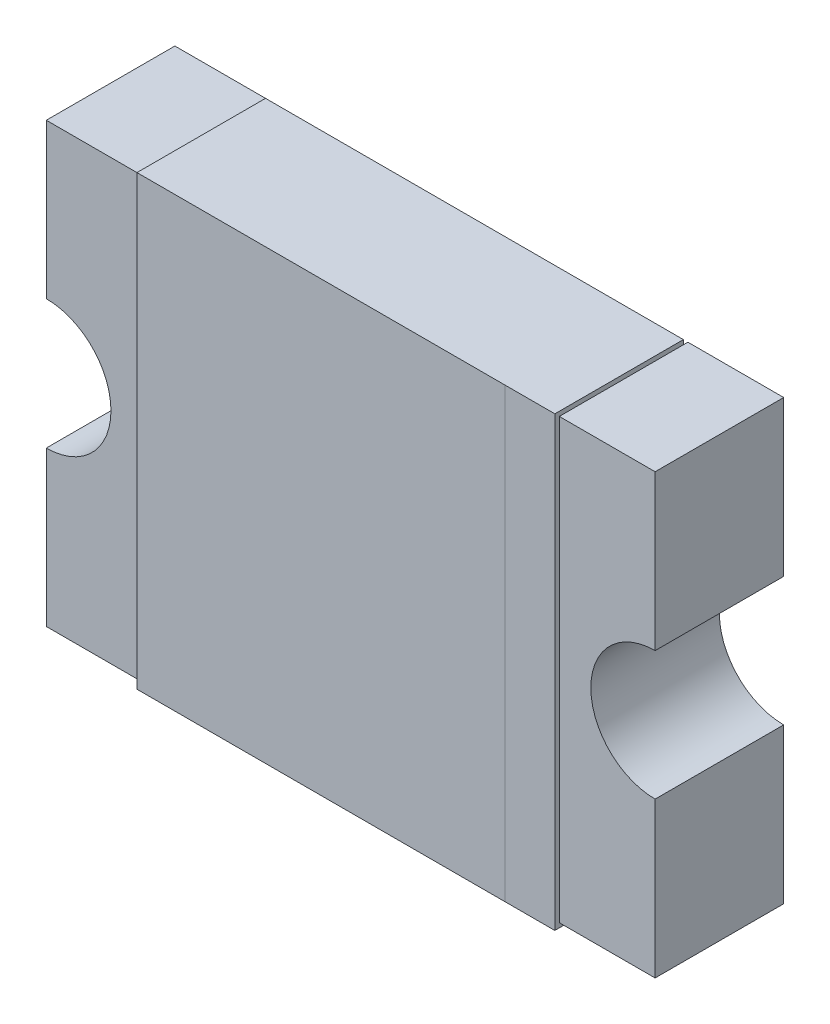
SolidWorks part; units mm, degrees
ref_plane "Plan de face" through (0, 0, 0) normal (0, 0, 1) x (1, 0, 0)
ref_plane "Plan de dessus" through (0, 0, 0) normal (0, 1, 0) x (1, 0, 0)
ref_plane "Plan de droite" through (0, 0, 0) normal (1, 0, 0) x (0, 0, -1)
sketch "Esquisse1" plane through (0, 0, 0) normal (0, 0, 1) x (1, 0, 0)
  line L1 (-2.365, 1.705) -> (2.37, 1.705)
  line L2 (-2.365, 1.705) -> (-2.365, -1.705)
  line L3 (-2.365, -1.705) -> (2.37, -1.705)
  line L4 (2.37, 1.705) -> (2.37, -1.705)
  dimension "D1" = 2.365
  dimension "D2" = 2.37
  dimension "D3" = 1.705
extrude "Extrusion1" add sketch "Esquisse1" along normal blind 1
sketch "Esquisse2" plane through (1.48, 0, 1) normal (0, 0, -1) x (0, 1, 0)
  line L0 (-1.705, 0.89) -> (1.705, 0.89) construction
  circle A0 centre (0, 0.89) radius 0.5
extrude "Enlèv. mat.-Extru.1" cut sketch "Esquisse2" along normal up to vertex (1 mm away)
sketch "Esquisse4" plane through (0, 0, 1) normal (0, 0, 1) x (1, 0, 0)
  line L0 (-2.365, 1.705) -> (-2.365, -1.705) construction
  circle A0 centre (-2.365, 0) radius 0.5029
extrude "Enlèv. mat.-Extru.2" cut sketch "Esquisse4" against normal up to vertex (1 mm away)
sketch "Esquisse8" plane through (0, 0, 1) normal (0, 0, 1) x (1, 0, 0)
  line L0 (2.37, 1.705) -> (-2.365, 1.705) construction
  line L1 (1.625, 1.705) -> (-1.625, 1.705)
  line L2 (1.625, 1.705) -> (1.625, -1.705)
  line L3 (1.625, -1.705) -> (-1.625, -1.705)
  line L4 (-1.625, 1.705) -> (-1.625, -1.705)
  line L5 (-2.365, -1.705) -> (2.37, -1.705) construction
  dimension "D1" = 1.625
  dimension "D2" = 3.25
extrude "Extrusion3" add sketch "Esquisse8" along normal blind 0.035
sketch "Esquisse10" plane through (0, 1.705, 0) normal (0, 1, 0) x (-1, 0, 0)
  line L0 (-2.37, 0) -> (2.365, 0) construction
  line L1 (1.625, 1.035) -> (-1.625, 1.035)
  line L2 (1.625, 1.035) -> (1.625, 0)
  line L3 (1.625, 0) -> (-1.625, 0)
  line L4 (-1.625, 1.035) -> (-1.625, 0)
extrude "Extrusion5" add sketch "Esquisse10" along normal blind 0.035
sketch "Esquisse11" plane through (0, -1.705, 0) normal (0, -1, 0) x (1, 0, 0)
  line L0 (-2.365, 0) -> (2.37, 0) construction
  line L1 (-1.625, 1.035) -> (1.625, 1.035)
  line L2 (-1.625, 1.035) -> (-1.625, 0)
  line L3 (-1.625, 0) -> (1.625, 0)
  line L4 (1.625, 1.035) -> (1.625, 0)
extrude "Extrusion6" add sketch "Esquisse11" along normal blind 0.035
sketch "Esquisse12" plane through (0, 0, 0) normal (0, 0, -1) x (1, 0, 0)
  line L1 (-1.625, 1.74) -> (1.625, 1.74)
  line L2 (-1.625, 1.74) -> (-1.625, -1.74)
  line L3 (-1.625, -1.74) -> (1.625, -1.74)
  line L4 (1.625, 1.74) -> (1.625, -1.74)
extrude "Enlèv. mat.-Extru.6" cut sketch "Esquisse12" against normal blind 0.035
sketch "Esquisse13" plane through (0, 0, 1.035) normal (0, 0, 1) x (1, 0, 0)
  line L0 (1.625, -1.74) -> (-1.625, -1.74) construction
  line L1 (1.625, 1.74) -> (1.2369, 1.74)
  line L2 (1.625, 1.74) -> (1.625, -1.74)
  line L3 (1.625, -1.74) -> (1.2369, -1.74)
  line L4 (1.2369, 1.74) -> (1.2369, -1.74)
extrude "Enlèv. mat.-Extru.7" cut sketch "Esquisse13" against normal blind 0.0001
